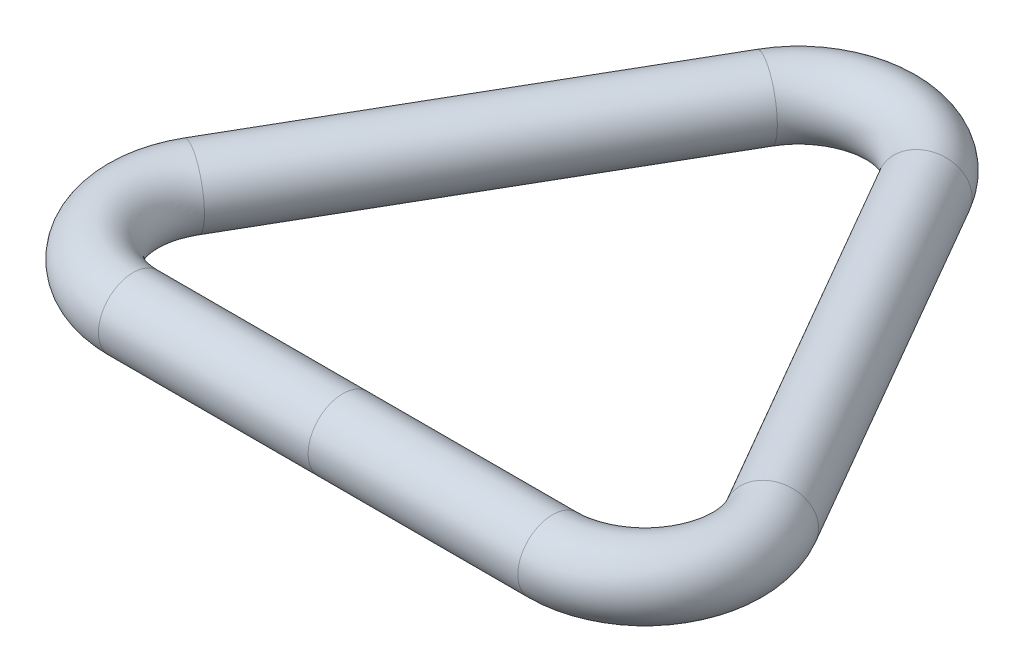
SolidWorks part; units mm, degrees
material "AISI 316 Annealed Stainless Steel Bar (SS)"
ref_plane "Front Plane" through (0, 0, 0) normal (0, 0, 1) x (1, 0, 0)
ref_plane "Top Plane" through (0, 0, 0) normal (0, 1, 0) x (1, 0, 0)
ref_plane "Right Plane" through (0, 0, 0) normal (1, 0, 0) x (0, 0, -1)
sketch "Sketch1" plane through (0, 0, 0) normal (0, 1, 0) x (1, 0, 0)
  line L1 (-10.9985, 39.6088) -> (-39.8015, -10.2794)
  line L2 (-28.803, -29.3294) -> (28.803, -29.3294)
  line L3 (39.8015, -10.2794) -> (10.9985, 39.6088)
  circle A0 centre (0, 0) radius 29.3294 construction
  arc A1 (-10.9985, 39.6088) -> (10.9985, 39.6088) centre (0, 33.2588) cw
  arc A2 (28.803, -29.3294) -> (39.8015, -10.2794) centre (28.803, -16.6294) ccw
  arc A3 (-28.803, -29.3294) -> (-39.8015, -10.2794) centre (-28.803, -16.6294) cw
  point P10 (50.8, -29.3294)
  point P13 (-50.8, -29.3294)
  dimension "D2" = 12.7
  dimension "D1" = 101.6
sketch "Sketch2" plane through (0, 0, 0) normal (1, 0, 0) x (0, 0, -1)
  circle A0 centre (-29.3294, 0) radius 4.7625
  dimension "D1" = 9.525
sweep "Sweep1" add profiles "Sketch2" path "Sketch1"
